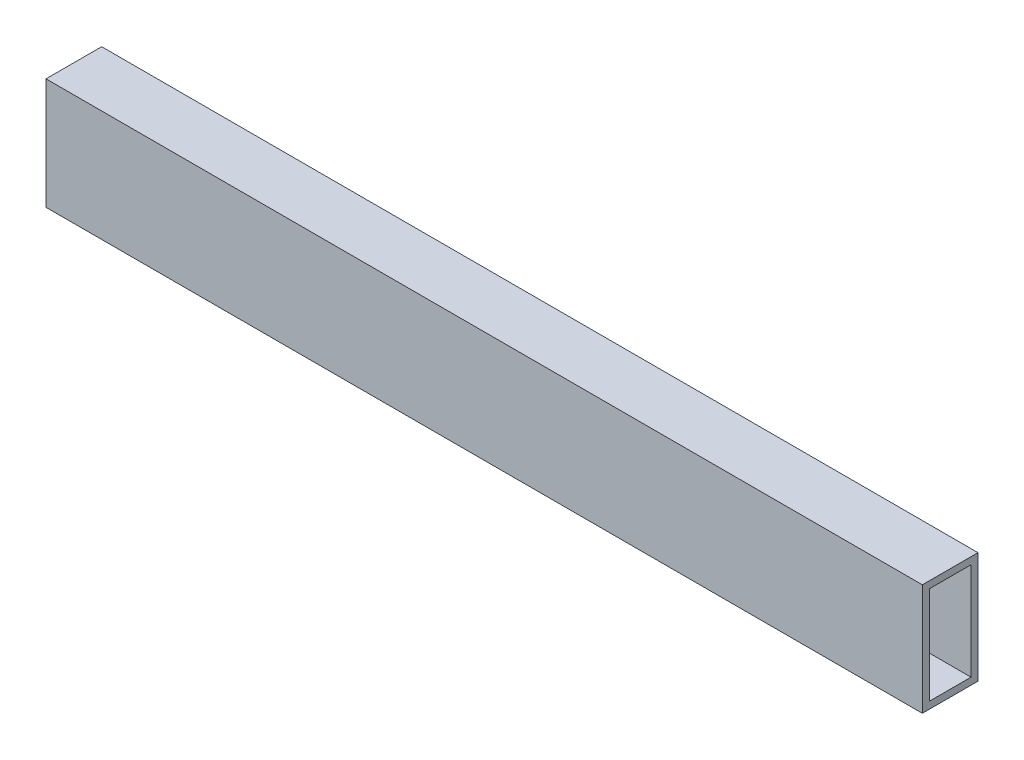
SolidWorks part; units mm, degrees
ref_plane "Front Plane" through (0, 0, 0) normal (0, 0, 1) x (1, 0, 0)
ref_plane "Top Plane" through (0, 0, 0) normal (0, 1, 0) x (1, 0, 0)
ref_plane "Right Plane" through (0, 0, 0) normal (1, 0, 0) x (0, 0, -1)
sketch "Sketch1" plane through (0, 0, 0) normal (1, 0, 0) x (0, 0, -1)
  line L1 (0, 0) -> (25.4, 0)
  line L2 (0, 0) -> (0, 50.8)
  line L3 (0, 50.8) -> (25.4, 50.8)
  line L4 (25.4, 0) -> (25.4, 50.8)
  line L5 (3.175, 47.625) -> (22.225, 47.625)
  line L6 (3.175, 47.625) -> (3.175, 3.175)
  line L7 (3.175, 3.175) -> (22.225, 3.175)
  line L8 (22.225, 47.625) -> (22.225, 3.175)
  dimension "D1" = 3.175
  dimension "D2" = 3.175
  dimension "D3" = 3.175
  dimension "D4" = 3.175
  dimension "D5" = 25.4
  dimension "D6" = 50.8
extrude "Boss-Extrude1" add sketch "Sketch1" along normal blind 400
